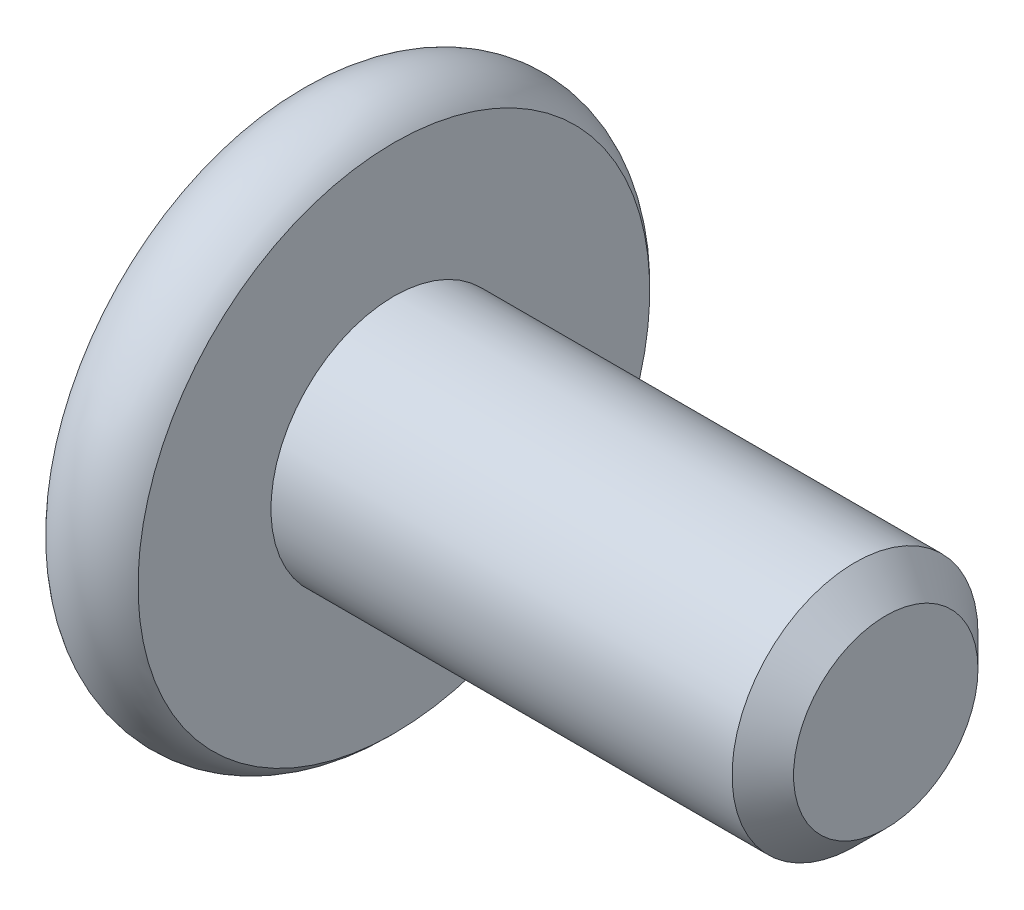
SolidWorks part; units mm, degrees
material "Plain Carbon Steel"
ref_plane "Front Plane" through (0, 0, 0) normal (0, 0, 1) x (1, 0, 0)
ref_plane "Top Plane" through (0, 0, 0) normal (0, 1, 0) x (1, 0, 0)
ref_plane "Right Plane" through (0, 0, 0) normal (1, 0, 0) x (0, 0, -1)
other "M5 x 15"
sketch "Sketch2" plane through (0, 0, 0) normal (1, 0, 0) x (0, 0, -1)
  circle A0 centre (0, 0) radius 2
  dimension "D1" = 4
extrude "Boss-Extrude1" add sketch "Sketch2" against normal blind 8
chamfer "Chamfer1" distance 0.5 angle 45 1 edges at (0, 0, -2)
sketch "Sketch6" plane through (0, 0, 0) normal (0, 0, 1) x (1, 0, 0)
  line L0 (-9.5, 0) -> (-9.5, 4.1614)
  line L1 (-9.5, 0) -> (-8, 0)
  line L2 (-8.75, 0) -> (-8.75, 3.5) construction
  line L6 (-8, 4.1614) -> (-8, 0)
  line L8 (-8, 0) -> (-14.6471, 0) construction
  line L10 (-8, 2) -> (-8, -2) construction
  arc A0 (-9.5, 4.1614) -> (-8, 4.1614) centre (-8.75, 3.5) cw
  dimension "D3" = 1
  dimension "D1" = 1.5
  dimension "D2" = 9
revolve "Revolve1" add sketch "Sketch6" angle 360 about L8
sketch "Sketch7" plane through (-9.5, 0, 0) normal (-1, 0, 0) x (0, 0, 1)
  line L1 (0, 1.7321) -> (-1.5, 0.866)
  line L2 (-1.5, 0.866) -> (-1.5, -0.866)
  line L3 (-1.5, -0.866) -> (0, -1.7321)
  line L4 (0, -1.7321) -> (1.5, -0.866)
  line L5 (1.5, -0.866) -> (1.5, 0.866)
  line L6 (1.5, 0.866) -> (0, 1.7321)
  circle A0 centre (0, 0) radius 1.5 construction
  dimension "D1" = 3
extrude "Cut-Extrude1" cut sketch "Sketch7" against normal blind 2.3
sketch "Sketch8" plane through (-9.5, 0, 0) normal (-1, 0, 0) x (0, 0, 1)
  circle A0 centre (0, 0) radius 1.7821
  dimension "D1" = 0.05
extrude "Cut-Extrude2" cut sketch "Sketch8" against normal blind 1 draft 45
